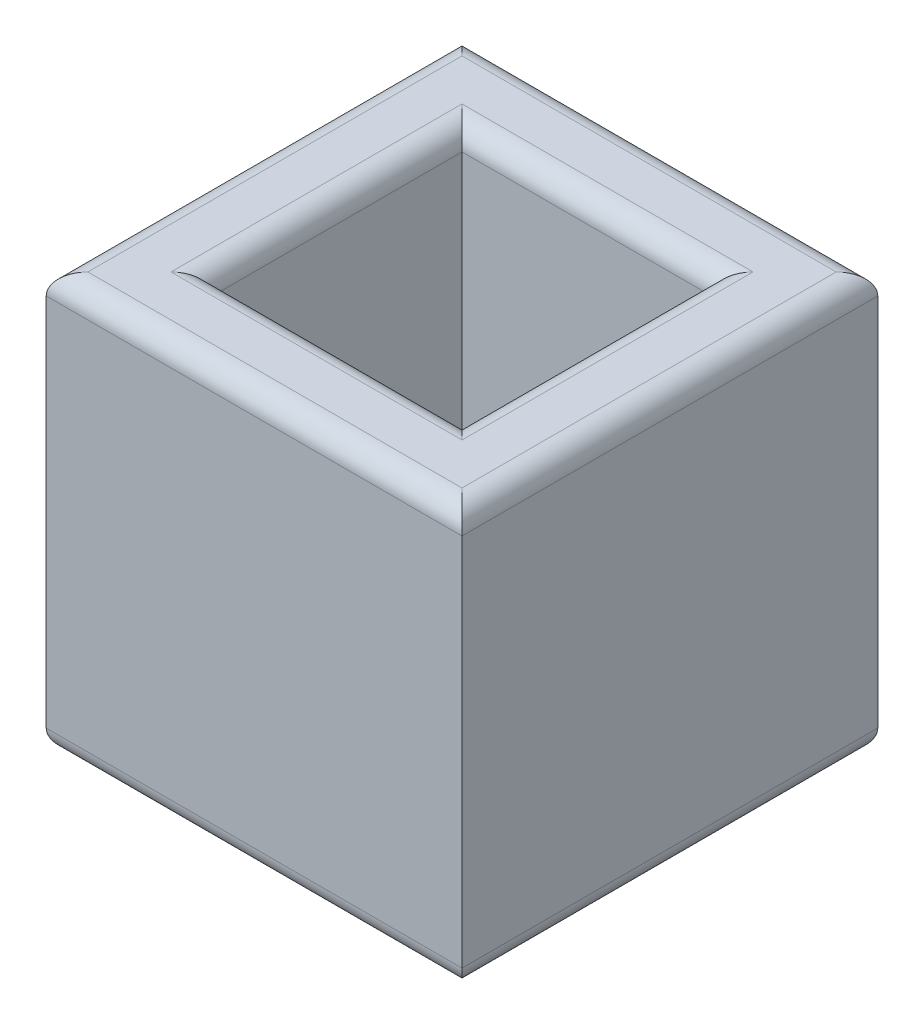
SolidWorks part; units mm, degrees
ref_plane "Front Plane" through (0, 0, 0) normal (0, 0, 1) x (1, 0, 0)
ref_plane "Top Plane" through (0, 0, 0) normal (0, 1, 0) x (1, 0, 0)
ref_plane "Right Plane" through (0, 0, 0) normal (1, 0, 0) x (0, 0, -1)
sketch "Sketch1" plane through (0, 0, 0) normal (0, 1, 0) x (1, 0, 0)
  line L1 (-63.5, -63.5) -> (63.5, -63.5)
  line L2 (-63.5, -63.5) -> (-63.5, 63.5)
  line L3 (-63.5, 63.5) -> (63.5, 63.5)
  line L4 (63.5, -63.5) -> (63.5, 63.5)
  line L5 (-63.5, -63.5) -> (63.5, 63.5) construction
  line L6 (-63.5, 63.5) -> (63.5, -63.5) construction
  point P0 (0, 0)
  dimension "D1" = 127
extrude "Boss-Extrude1" add sketch "Sketch1" along normal blind 127 contours L3 L4 L1 L2
sketch "Sketch2" plane through (0, 127, 0) normal (0, 1, 0) x (1, 0, 0)
  line L1 (-38.1, -38.1) -> (38.1, -38.1)
  line L2 (-38.1, -38.1) -> (-38.1, 38.1)
  line L3 (-38.1, 38.1) -> (38.1, 38.1)
  line L4 (38.1, -38.1) -> (38.1, 38.1)
  line L5 (-38.1, -38.1) -> (38.1, 38.1) construction
  line L6 (-38.1, 38.1) -> (38.1, -38.1) construction
  point P0 (0, 0)
  dimension "D1" = 76.2
extrude "Cut-Extrude1" cut sketch "Sketch2" against normal through all both and the other way through all
fillet "Fillet3" radius 6.35 16 edges at (0, 0, 63.5) (63.5, 0, 0) (0, 0, -63.5) (-63.5, 0, 0) (0, 0, 38.1) (-38.1, 0, 0) (0, 0, -38.1) (38.1, 0, 0) (0, 127, 63.5) (-63.5, 127, 0) (-38.1, 127, 0) (0, 127, 38.1) (38.1, 127, 0) (0, 127, -38.1) (0, 127, -63.5) (63.5, 127, 0)
